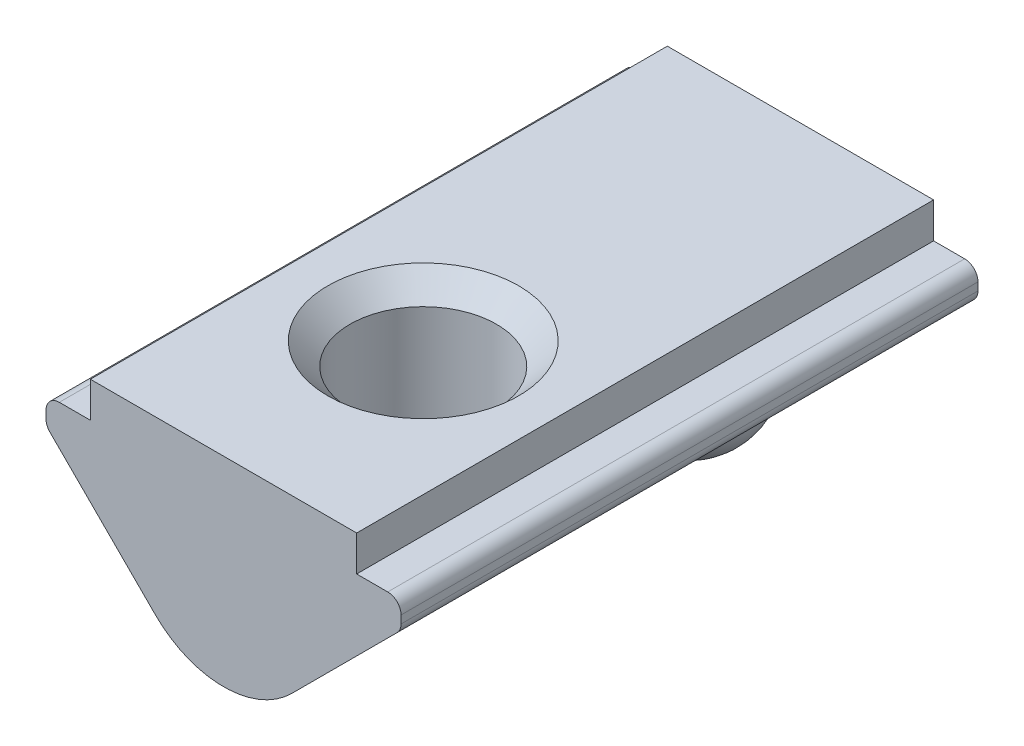
SolidWorks part; units mm, degrees
ref_plane "Спереди" through (0, 0, 0) normal (0, 0, 1) x (1, 0, 0)
ref_plane "Сверху" through (0, 0, 0) normal (0, 1, 0) x (1, 0, 0)
ref_plane "Справа" through (0, 0, 0) normal (1, 0, 0) x (0, 0, -1)
sketch "Эскиз1" plane through (0, 0, 0) normal (0, 0, 1) x (1, 0, 0)
  line L0 (-3, 0) -> (3, 0)
  line L2 (4, -1.4) -> (1.5364, -3.8636)
  line L3 (-1.5364, -3.8636) -> (-4, -1.4)
  line L5 (-3, 0) -> (-3, -0.8)
  line L6 (-3, -0.8) -> (-4, -0.8)
  line L7 (-4, -0.8) -> (-4, -1.4)
  line L8 (3, 0) -> (3, -0.8)
  line L9 (3, -0.8) -> (4, -0.8)
  line L10 (4, -0.8) -> (4, -1.4)
  arc A0 (1.5364, -3.8636) -> (-1.5364, -3.8636) centre (0, -2.3272) cw
  point P4 (0, 0)
  dimension "D1" = 6
  dimension "D2" = 8
  dimension "D3" = 0.8
  dimension "D4" = 45
  dimension "D5" = 0.6
  dimension "D6" = 4.5
extrude "Бобышка-Вытянуть1" add sketch "Эскиз1" along normal mid plane 13
hole_wizard "Отверстие обработанное метчиком M41" positions "Эскиз2" profile "Эскиз4" tap size "M4" standard "ISO" end condition through all
sketch "Эскиз2" plane through (0, 0, 0) normal (0, 1, 0) x (1, 0, 0)
  line L0 (3, -6.5) -> (-3, -6.5) construction
  point P0 (0, -2)
  dimension "D1" = 4.5
sketch "Эскиз4" plane through (0, 0, 2) normal (1, 0, 0) x (0, 0, 1)
  line L0 (0, 0) -> (0, 4.5)
  line L1 (0, 4.5) -> (1.65, 4.5)
  line L2 (1.65, 4.5) -> (1.65, 0.5)
  line L3 (1.65, 0.5) -> (2.15, 0)
  line L5 (2.15, 0) -> (0, 0)
  line L6 (-1.65, 0.5) -> (-2.15, 0) construction
  line L11 (0, -6.35) -> (0, 107.95) construction
  dimension "Диаметр проходного сверла" = 3.3
  dimension "Глубина проходного сверла" = 4.5
  dimension "Диаметр передней зенковки" = 4.3
  dimension "Угол передней зенковки" = 90
cosmetic thread "Отверстие резьбы1" parameters "D2"=4
sketch "Эскиз5" plane through (0, 0, 0) normal (1, 0, 0) x (0, 0, -1)
  line L0 (-6.5, 0) -> (6.5, 0) construction
  line L1 (4, -2) -> (4, -5) construction
  line L2 (6.5, -3.8636) -> (6.5, -1.4) construction
  line L3 (4, -2) -> (4, -5)
  arc A0 (4, -2) -> (4, -5) centre (4, -3.5) ccw
  dimension "D3" = 1.5
  dimension "D1" = 5
  dimension "D2" = 2.5
revolve "Повернуть1" add sketch "Эскиз5" angle 360 about L1
fillet "Скругление1" radius 0.3 4 edges at (4, -1.4, 0) (4, -0.8, 0) (-4, -0.8, 0) (-4, -1.4, 0)
